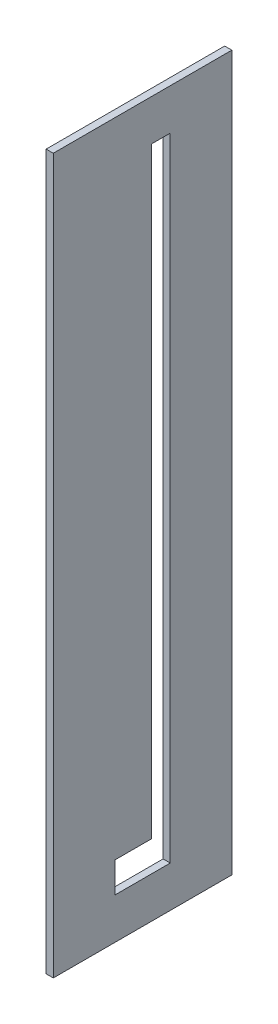
SolidWorks part; units mm, degrees
ref_plane "Front Plane" through (0, 0, 0) normal (0, 0, 1) x (1, 0, 0)
ref_plane "Top Plane" through (0, 0, 0) normal (0, 1, 0) x (1, 0, 0)
ref_plane "Right Plane" through (0, 0, 0) normal (1, 0, 0) x (0, 0, -1)
sketch "Sketch1" plane through (0, 0, 0) normal (1, 0, 0) x (0, 0, -1)
  line L0 (-63.0724, 0) -> (63.0724, 0) construction
  line L1 (-15.5, 23) -> (15.5, 23)
  line L2 (-13.5, 375) -> (13.5, 375) construction
  line L3 (-13.5, 375) -> (-13.5, 25) construction
  line L4 (-13.5, 25) -> (13.5, 25) construction
  line L5 (13.5, 375) -> (13.5, 25) construction
  line L6 (-13.5, 375) -> (13.5, 25) construction
  line L7 (-13.5, 25) -> (13.5, 375) construction
  line L8 (15.5, 377) -> (15.5, 23)
  line L9 (-15.5, 377) -> (15.5, 377)
  line L10 (-15.5, 377) -> (-15.5, 23)
  line L11 (-50, 0) -> (50, 0)
  line L12 (-50, 0) -> (-50, 400)
  line L13 (-50, 400) -> (50, 400)
  line L14 (50, 400) -> (50, 0)
  point P0 (0, 200)
  point P4 (0, 0)
  point P18 (0, 0)
  dimension "D1" = 25
  dimension "D2" = 27
  dimension "D3" = 23
  dimension "D5" = 100
  dimension "D6" = 350
  dimension "D4" = 2
extrude "Boss-Extrude1" add sketch "Sketch1" along normal blind 4
sketch "Sketch2" plane through (0, 0, 0) normal (-1, 0, 0) x (0, 0, 1)
  line L0 (-15.5, 377) -> (15.5, 377) construction
  line L1 (15.5, 377) -> (15.5, 23) construction
  line L2 (-15.5, 377) -> (15.5, 377)
  line L3 (15.5, 377) -> (15.5, 23)
  line L4 (15.5, 40) -> (-5, 40)
  line L5 (-5, 40) -> (-5, 377)
  line M6 (15.5, 377) -> (15.5, 23)
  dimension "D1" = 17
  dimension "D2" = 20.5
extrude "Boss-Extrude2" add sketch "Sketch2" against normal blind 4 contours L5 L4 L2 M6
